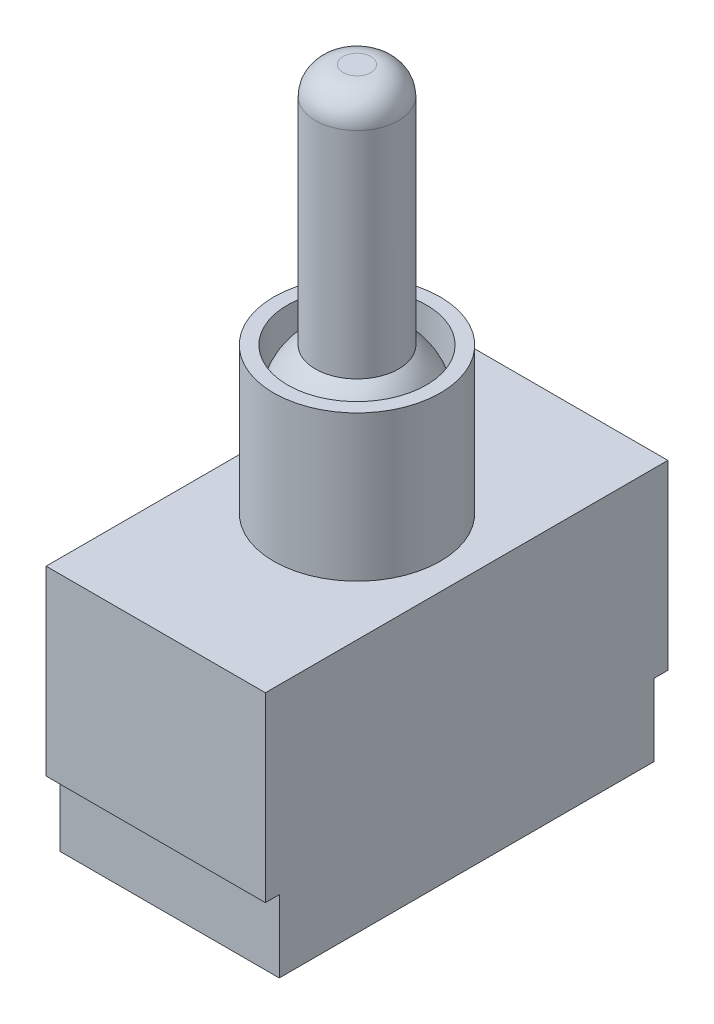
SolidWorks part; units mm, degrees
ref_plane "Спереди" through (0, 0, 0) normal (0, 0, 1) x (1, 0, 0)
ref_plane "Сверху" through (0, 0, 0) normal (0, 1, 0) x (1, 0, 0)
ref_plane "Справа" through (0, 0, 0) normal (1, 0, 0) x (0, 0, -1)
sketch "Sketch1" plane through (0, 0, 0) normal (0, 1, 0) x (1, 0, 0)
  line L1 (7.9, -14.5) -> (-7.9, -14.5)
  line L2 (7.9, -14.5) -> (7.9, 14.5)
  line L3 (7.9, 14.5) -> (-7.9, 14.5)
  line L4 (-7.9, -14.5) -> (-7.9, 14.5)
  line L5 (7.9, -14.5) -> (-7.9, 14.5) construction
  line L6 (7.9, 14.5) -> (-7.9, -14.5) construction
  point P0 (0, 0)
  dimension "D1" = 15.8
  dimension "D2" = 29
extrude "Boss-Extrude1" add sketch "Sketch1" along normal blind 13.1
sketch "Sketch2" plane through (0, 13.1, 0) normal (0, 1, 0) x (1, 0, 0)
  line L0 (-7.9, 14.5) -> (7.9, -14.5) construction
  circle A0 centre (0, 0) radius 6
  dimension "D1" = 12
extrude "Boss-Extrude2" add sketch "Sketch2" along normal blind 10.5
sketch "Sketch4" plane through (0, 23.6, 0) normal (0, 1, 0) x (1, 0, 0)
  circle A0 centre (0, 0) radius 5
  dimension "D1" = 10
extrude "Cut-Extrude1" cut sketch "Sketch4" against normal blind 4
sketch "Sketch5" plane through (0, 19.6, 0) normal (0, 1, 0) x (1, 0, 0)
  circle A0 centre (0, 0) radius 3
  dimension "D1" = 6
extrude "Boss-Extrude3" add sketch "Sketch5" along normal blind 21.5
sketch "Sketch3" plane through (0, 19.6, 0) normal (0, 1, 0) x (1, 0, 0)
  line L0 (0, -6) -> (0, 6) construction
  line L1 (0, -5) -> (0, 5)
  circle A0 centre (0, 0) radius 6 construction
  arc A1 (0, -5) -> (0, 5) centre (0, 0) cw
  point P7 (0, 0)
  dimension "D1" = 10
revolve "Revolve2" add sketch "Sketch3" angle 180 about L0
fillet "Fillet1" radius 2 1 edges at (0, 41.1, 3)
sketch "Sketch6" plane through (0, 0, 0) normal (0, -1, 0) x (1, 0, 0)
  line L0 (-7.9, -14.5) -> (-7.9, 14.5) construction
  line L1 (7.9, 13.5) -> (-7.9, 13.5)
  line L2 (7.9, 13.5) -> (7.9, -13.5)
  line L3 (7.9, -13.5) -> (-7.9, -13.5)
  line L4 (-7.9, 13.5) -> (-7.9, -13.5)
  line L5 (7.9, 13.5) -> (-7.9, -13.5) construction
  line L6 (7.9, -13.5) -> (-7.9, 13.5) construction
  point P0 (0, 0)
  dimension "D1" = 27
extrude "Boss-Extrude4" add sketch "Sketch6" along normal blind 5.2
